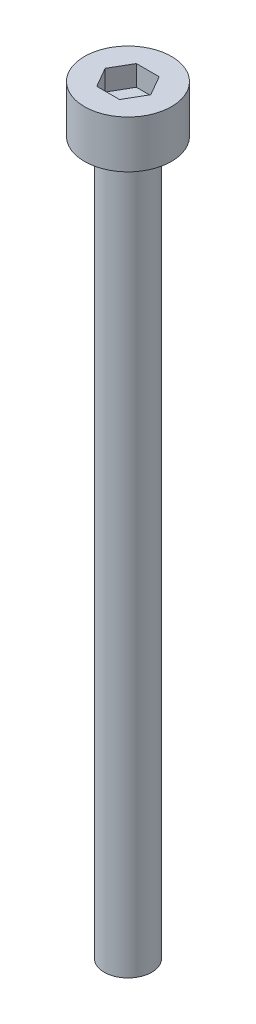
SolidWorks part; units mm, degrees
material "AISI 304"
ref_plane "前视基准面" through (0, 0, 0) normal (0, 0, 1) x (1, 0, 0)
ref_plane "上视基准面" through (0, 0, 0) normal (0, 1, 0) x (1, 0, 0)
ref_plane "右视基准面" through (0, 0, 0) normal (1, 0, 0) x (0, 0, -1)
sketch "草图1" plane through (0, 0, 0) normal (0, 1, 0) x (1, 0, 0)
  circle A0 centre (0, 0) radius 2.75
  dimension "D1" = 5.5
extrude "杯头" add sketch "草图1" along normal blind 3
sketch "草图2" plane through (0, 3, 0) normal (0, 1, 0) x (1, 0, 0)
  line L1 (1.4434, 0) -> (0.7217, 1.25)
  line L2 (0.7217, 1.25) -> (-0.7217, 1.25)
  line L3 (-0.7217, 1.25) -> (-1.4434, 0)
  line L4 (-1.4434, 0) -> (-0.7217, -1.25)
  line L5 (-0.7217, -1.25) -> (0.7217, -1.25)
  line L6 (0.7217, -1.25) -> (1.4434, 0)
  circle A0 centre (0, 0) radius 1.25 construction
  dimension "D1" = 2.5
extrude "内六角口" cut sketch "草图2" against normal blind 1.3
sketch "草图3" plane through (0, 0, 0) normal (0, -1, 0) x (1, 0, 0)
  circle A0 centre (0, 0) radius 1.5
  dimension "D1" = 3
extrude "螺纹长" add sketch "草图3" along normal blind 45
